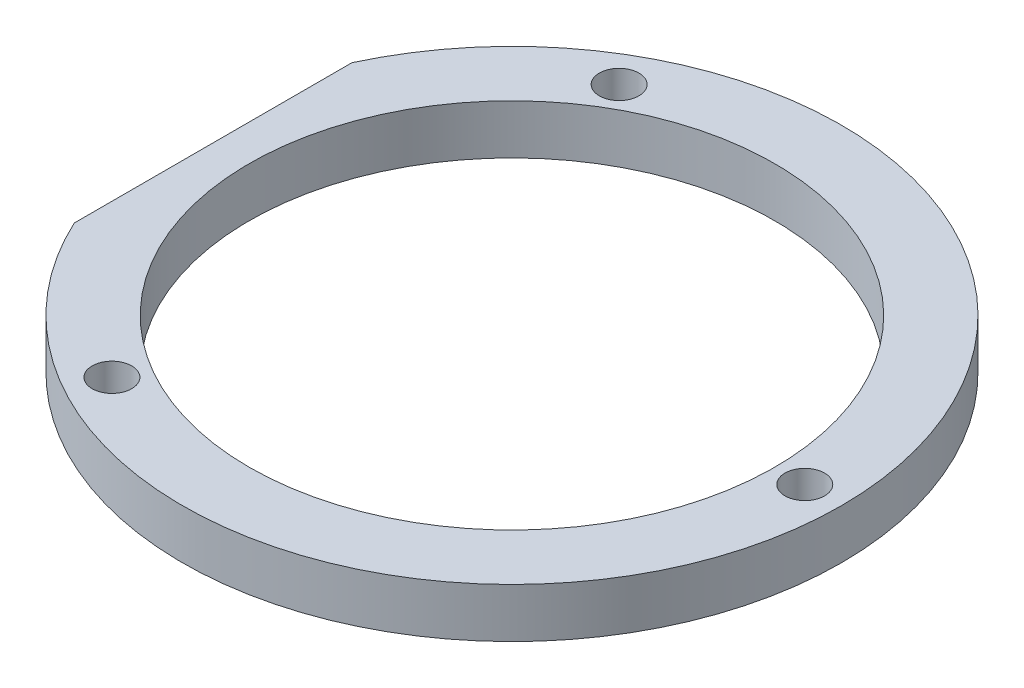
SolidWorks part; units mm, degrees
material "尼龙 101"
ref_plane "前视基准面" through (0, 0, 0) normal (0, 0, 1) x (1, 0, 0)
ref_plane "上视基准面" through (0, 0, 0) normal (0, 1, 0) x (1, 0, 0)
ref_plane "右视基准面" through (0, 0, 0) normal (1, 0, 0) x (0, 0, -1)
sketch "草图1" plane through (0, 0, 0) normal (0, 1, 0) x (1, 0, 0)
  circle A0 centre (0, 0) radius 26.64
  dimension "D1" = 53.28
extrude "凸台-拉伸1" add sketch "草图1" along normal blind 4
sketch "草图2" plane through (0, 4, 0) normal (0, 1, 0) x (1, 0, 0)
  circle A0 centre (0, 0) radius 21.25
  dimension "D1" = 42.5
extrude "切除-拉伸1" cut sketch "草图2" against normal blind 4
sketch "草图3" plane through (0, 4, 0) normal (0, 1, 0) x (1, 0, 0)
  circle A0 centre (23.6721, 0) radius 1.6
  circle A1 centre (0, 0) radius 26.64 construction
  dimension "D1" = 23.6721
  dimension "D2" = 3.2
extrude "切除-拉伸2" cut sketch "草图3" against normal blind 4
pattern_circular "阵列(圆周)1" count 3 over 360 about axis through (0, 0, 0) along (0, 1, 0) of "切除-拉伸2"
sketch "草图5" plane through (0, 4, 0) normal (0, 1, 0) x (1, 0, 0)
  line L1 (-41.3635, -30.807) -> (-24.16, -30.807)
  line L2 (-41.3635, -30.807) -> (-41.3635, 28.2936)
  line L3 (-41.3635, 28.2936) -> (-24.16, 28.2936)
  line L4 (-24.16, -30.807) -> (-24.16, 28.2936)
  circle A0 centre (0, 0) radius 21.25 construction
  dimension "D1" = 24.16
extrude "切除-拉伸3" cut sketch "草图5" against normal blind 4
